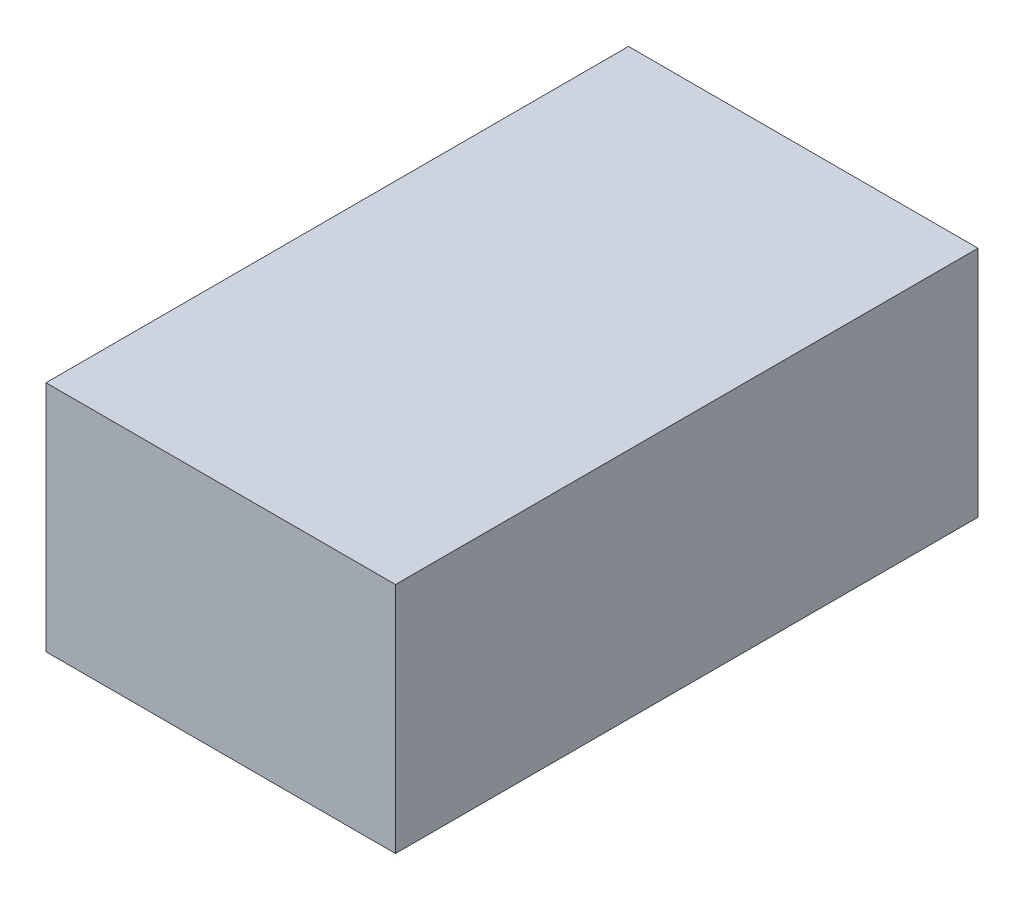
SolidWorks part; units mm, degrees
ref_plane "Front Plane" through (0, 0, 0) normal (0, 0, 1) x (1, 0, 0)
ref_plane "Top Plane" through (0, 0, 0) normal (0, 1, 0) x (1, 0, 0)
ref_plane "Right Plane" through (0, 0, 0) normal (1, 0, 0) x (0, 0, -1)
sketch "BaseS" plane through (0, 0, 0) normal (0, 1, 0) x (1, 0, 0)
  line L1 (-0.3, 0.5) -> (0.3, 0.5)
  line L2 (-0.3, 0.5) -> (-0.3, -0.5)
  line L3 (-0.3, -0.5) -> (0.3, -0.5)
  line L4 (0.3, 0.5) -> (0.3, -0.5)
  line L5 (-0.3, 0.5) -> (0.3, -0.5) construction
  line L6 (-0.3, -0.5) -> (0.3, 0.5) construction
  point P0 (0, 0)
  dimension "Length" = 1
  dimension "Width" = 0.6
extrude "Base" add sketch "BaseS" along normal blind 0.4
